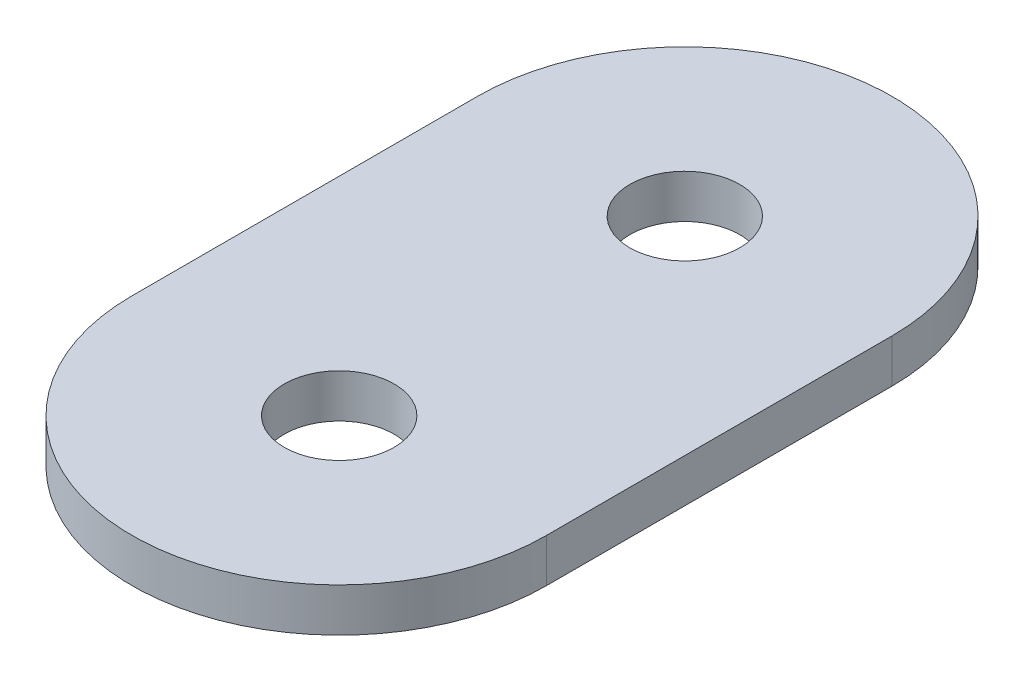
SolidWorks part; units mm, degrees
material "Alum Plate"
ref_plane "Front Plane" through (0, 0, 0) normal (0, 0, 1) x (1, 0, 0)
ref_plane "Top Plane" through (0, 0, 0) normal (0, 1, 0) x (1, 0, 0)
ref_plane "Right Plane" through (0, 0, 0) normal (1, 0, 0) x (0, 0, -1)
other "Bounding Box"
ref_plane "Default Plane" through (13.8565, 3.175, 6.7999) normal (0, -1, 0) x (-1, 0, 0)
sketch "Sketch1" plane through (0, 0, 0) normal (0, 1, 0) x (1, 0, 0)
  line L0 (0, -6.35) -> (0, 0) construction
  line L1 (0, 0) -> (0, 6.35) construction
  line L2 (-7.62, -6.35) -> (-7.62, 6.35)
  line L3 (7.62, 6.35) -> (7.62, -6.35)
  circle A0 centre (0, 6.35) radius 2.0193
  circle A1 centre (0, -6.35) radius 2.0193
  arc A2 (-7.62, 6.35) -> (7.62, 6.35) centre (0, 6.35) cw
  arc A3 (7.62, -6.35) -> (-7.62, -6.35) centre (0, -6.35) cw
  dimension "D2" = 4.0386
  dimension "D3" = 7.62
  dimension "D1" = 12.7
extrude "Boss-Extrude1" add sketch "Sketch1" along normal mid plane 1.6002
